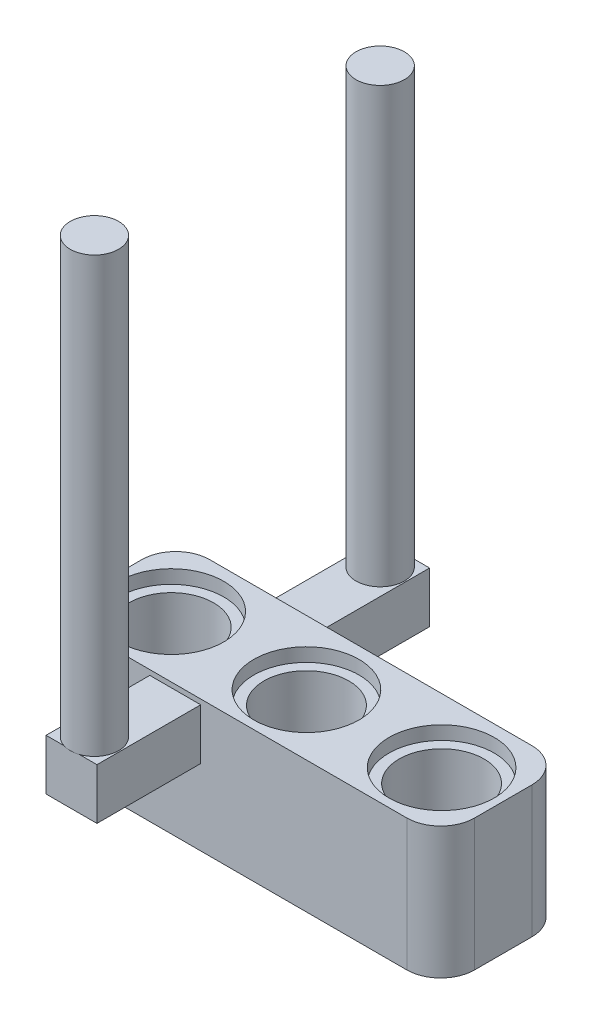
SolidWorks part; units mm, degrees
ref_plane "Front Plane" through (0, 0, 0) normal (0, 0, 1) x (1, 0, 0)
ref_plane "Top Plane" through (0, 0, 0) normal (0, 1, 0) x (1, 0, 0)
ref_plane "Right Plane" through (0, 0, 0) normal (1, 0, 0) x (0, 0, -1)
sketch "Sketch3" plane through (0, 0, 0) normal (0, 1, 0) x (1, 0, 0)
  line L1 (0, 0) -> (-23, 0)
  line L2 (0, 0) -> (0, 7.38)
  line L3 (0, 7.38) -> (-23, 7.38)
  line L4 (-23, 0) -> (-23, 7.38)
  dimension "D1" = 23
  dimension "D2" = 7.38
extrude "Boss-Extrude1" add sketch "Sketch3" along normal blind 7.76
sketch "Sketch4" plane through (0, 0, 0) normal (0, -1, 0) x (-1, 0, 0)
  line L0 (23, 0) -> (0, 0) construction
  circle A0 centre (19.5383, 3.69) radius 3.1
  circle A1 centre (11.5383, 3.69) radius 3.1
  circle A2 centre (3.5383, 3.69) radius 3.1
  dimension "D1" = 6.2
  dimension "D2" = 3.69
  dimension "D3" = 3
extrude "Cut-Extrude2" cut sketch "Sketch4" against normal blind 0.8
sketch "Sketch6" plane through (0, 0.8, 0) normal (0, -1, 0) x (-1, 0, 0)
  circle A0 centre (3.5383, 3.5915) radius 2.5
  circle A1 centre (3.5383, 3.69) radius 3.1 construction
  circle A2 centre (11.5083, 3.5915) radius 2.5
  circle A3 centre (19.4783, 3.5915) radius 2.5
  dimension "D2" = 5
  dimension "D1" = 0
  dimension "D3" = 3
sketch "Sketch7" plane through (0, 7.76, 0) normal (0, 1, 0) x (1, 0, 0)
  circle A0 centre (-19.4783, 3.5915) radius 3.1
  circle A3 centre (-11.5083, 3.5915) radius 3.1
  circle A4 centre (-3.5383, 3.5915) radius 3.1
  dimension "D1" = 6.2
  dimension "D2" = 3
extrude "Cut-Extrude3" cut sketch "Sketch7" against normal blind 0.8
extrude "Cut-Extrude4" cut sketch "Sketch6" against normal through all
fillet "Fillet3" radius 2 1 edges at (0, 3.88, 0)
fillet "Fillet4" radius 2 1 edges at (-23, 3.88, 0)
fillet "Fillet5" radius 2 1 edges at (-23, 3.88, -7.38)
fillet "Fillet6" radius 2 1 edges at (0, 3.88, -7.38)
sketch "Sketch8" plane through (0, 0, -7.38) normal (0, 0, -1) x (-1, 0, 0)
  line L0 (21, 0) -> (21, 7.76) construction
  line L1 (14.15, 4.7003) -> (17.15, 4.7003)
  line L2 (14.15, 4.7003) -> (14.15, 7.7003)
  line L3 (14.15, 7.7003) -> (17.15, 7.7003)
  line L4 (17.15, 4.7003) -> (17.15, 7.7003)
  dimension "D1" = 3.85
  dimension "D2" = 3
  dimension "D3" = 3
extrude "Boss-Extrude2" add sketch "Sketch8" along normal blind 6.115
sketch "Sketch9" plane through (0, 7.7003, 0) normal (0, 1, 0) x (1, 0, 0)
  line L0 (-17.15, 13.495) -> (-17.15, 7.38) construction
  circle A0 centre (-15.65, 12.082) radius 1.425
  dimension "D2" = 2.85
  dimension "D1" = 1.5
extrude "Boss-Extrude3" add sketch "Sketch9" along normal blind 25.6
sketch "Sketch12" plane through (0, 0, 0) normal (0, 0, 1) x (1, 0, 0)
  line L0 (-21, 7.76) -> (-21, 0) construction
  line L1 (-17.15, 7.4628) -> (-14.15, 7.4628)
  line L2 (-17.15, 7.4628) -> (-17.15, 4.4628)
  line L3 (-17.15, 4.4628) -> (-14.15, 4.4628)
  line L4 (-14.15, 7.4628) -> (-14.15, 4.4628)
  dimension "D1" = 3
  dimension "D2" = 3
  dimension "D3" = 3.85
extrude "Boss-Extrude4" add sketch "Sketch12" along normal blind 6.115
sketch "Sketch13" plane through (0, 7.4628, 0) normal (0, 1, 0) x (1, 0, 0)
  line L0 (-14.15, -6.115) -> (-14.15, 0) construction
  circle A0 centre (-15.65, -4.7633) radius 1.425
  dimension "D1" = 1.5
  dimension "D2" = 2.85
extrude "Boss-Extrude5" add sketch "Sketch13" along normal blind 25.6
